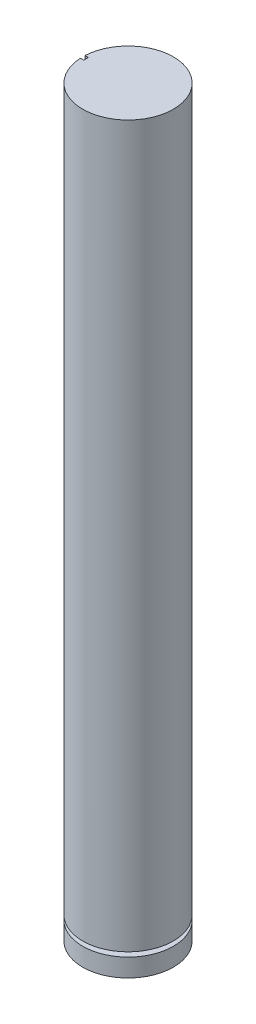
SolidWorks part; units mm, degrees
ref_plane "Front Plane" through (0, 0, 0) normal (0, 0, 1) x (1, 0, 0)
ref_plane "Top Plane" through (0, 0, 0) normal (0, 1, 0) x (1, 0, 0)
ref_plane "Right Plane" through (0, 0, 0) normal (1, 0, 0) x (0, 0, -1)
sketch "Sketch1" plane through (0, 0, 0) normal (0, 1, 0) x (1, 0, 0)
  circle A0 centre (0, 0) radius 2
  dimension "D1" = 4
extrude "Boss-Extrude1" add sketch "Sketch1" along normal blind 32.766
sketch "Sketch2" plane through (0, 0, 0) normal (1, 0, 0) x (0, 0, -1)
  line L0 (2, 0) -> (2, 32.766) construction
  line L1 (2, 1) -> (1.5, 1)
  line L2 (2, 1) -> (2, 0.8)
  line L3 (2, 0.8) -> (1.5, 0.8)
  line L4 (1.5, 1) -> (1.5, 0.8)
  line L5 (-2, 0) -> (2, 0) construction
  line L6 (0, 0) -> (0, 4.8308) construction
  dimension "D1" = 0.5
  dimension "D2" = 0.2
  dimension "D3" = 0.8
revolve "Cut-Revolve1" cut sketch "Sketch2" angle 360 about L6
sketch "Sketch3" plane through (0, 32.766, 0) normal (0, 1, 0) x (1, 0, 0)
  line L0 (0, 0) -> (-2, 0) construction
  line L2 (-2, 0.1) -> (-1.85, 0.1)
  line L3 (-2, 0.1) -> (-2, -0.1)
  line L4 (-2, -0.1) -> (-1.85, -0.1)
  line L5 (-1.85, 0.1) -> (-1.85, -0.1)
  circle A0 centre (0, 0) radius 2 construction
  dimension "D1" = 0.2
  dimension "D2" = 0.15
extrude "Cut-Extrude1" cut sketch "Sketch3" against normal blind 3
